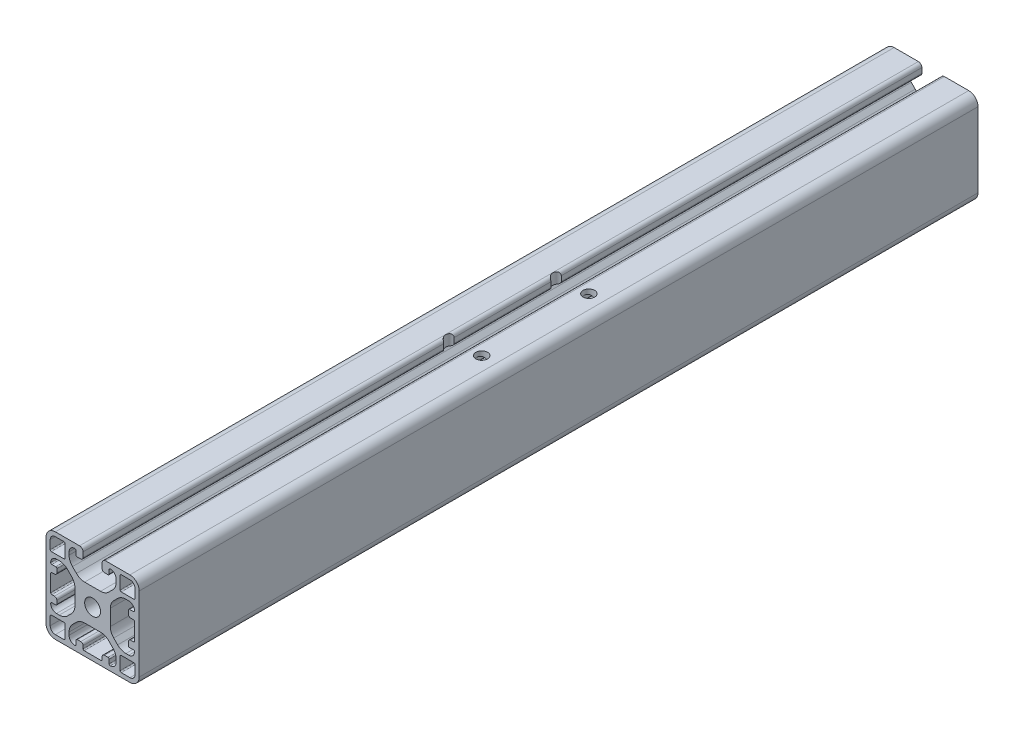
SolidWorks part; units mm, degrees
ref_plane "Ebene vorne" through (0, 0, 0) normal (0, 0, 1) x (1, 0, 0)
ref_plane "Ebene oben" through (0, 0, 0) normal (0, 1, 0) x (1, 0, 0)
ref_plane "Ebene rechts" through (0, 0, 0) normal (1, 0, 0) x (0, 0, -1)
ref_plane "Ebene1" through (0, 0, 1000) normal (0, 0, 1) x (1, 0, 0)
sketch "Skizze1" plane through (0, 0, 1000) normal (0, 0, 1) x (1, 0, 0)
  line L0 (0, 38.2) -> (3.7, 38.2)
  line L1 (4.2, 37.7) -> (4.2, 32.3)
  line L2 (3.7, 31.8) -> (-1.7, 31.8)
  line L3 (-2.2, 32.3) -> (-2.2, 36)
  line L4 (-2.2, 4) -> (-2.2, 7.7)
  line L5 (-1.7, 8.2) -> (3.7, 8.2)
  line L6 (4.2, 7.7) -> (4.2, 2.3)
  line L7 (3.7, 1.8) -> (0, 1.8)
  line L8 (32, 1.8) -> (28.3, 1.8)
  line L9 (27.8, 2.3) -> (27.8, 7.7)
  line L10 (28.3, 8.2) -> (33.7, 8.2)
  line L11 (34.2, 7.7) -> (34.2, 4)
  line L12 (34.2, 36) -> (34.2, 32.3)
  line L13 (33.7, 31.8) -> (28.3, 31.8)
  line L14 (27.8, 32.3) -> (27.8, 37.7)
  line L15 (28.3, 38.2) -> (32, 38.2)
  line L16 (12.5924, 12.4) -> (19.4076, 12.4)
  line L17 (22.9431, 10.9355) -> (24.6355, 9.2431)
  line L18 (26.1, 5.7076) -> (26.1, 4.5)
  line L19 (23.1, 2.5) -> (23.1, 4.15)
  line L20 (22.6, 4.65) -> (21.1, 4.65)
  line L21 (20.1, 3.65) -> (20.1, 2.5)
  line L22 (19.6, 2) -> (12.4, 2)
  line L23 (11.9, 2.5) -> (11.9, 3.65)
  line L24 (10.9, 4.65) -> (9.4, 4.65)
  line L25 (8.9, 4.15) -> (8.9, 2.5)
  line L26 (5.9, 4.5) -> (5.9, 5.7076)
  line L27 (7.3645, 9.2431) -> (9.0569, 10.9355)
  line L28 (-0.35, 15.9) -> (-1.5, 15.9)
  line L29 (-2, 16.4) -> (-2, 23.6)
  line L30 (-1.5, 24.1) -> (-0.35, 24.1)
  line L31 (0.65, 25.1) -> (0.65, 26.6)
  line L32 (0.15, 27.1) -> (-1.5, 27.1)
  line L33 (0.5, 30.1) -> (1.7076, 30.1)
  line L34 (5.2431, 28.6355) -> (6.9355, 26.9431)
  line L35 (8.4, 23.4076) -> (8.4, 16.5924)
  line L36 (6.9355, 13.0569) -> (5.2431, 11.3645)
  line L37 (1.7076, 9.9) -> (0.5, 9.9)
  line L38 (-1.5, 12.9) -> (0.15, 12.9)
  line L39 (0.65, 13.4) -> (0.65, 14.9)
  line L40 (23.6, 16.5924) -> (23.6, 23.4076)
  line L41 (25.0645, 26.9431) -> (26.7569, 28.6355)
  line L42 (30.2924, 30.1) -> (31.5, 30.1)
  line L43 (33.5, 27.1) -> (31.85, 27.1)
  line L44 (31.35, 26.6) -> (31.35, 25.1)
  line L45 (32.35, 24.1) -> (33.5, 24.1)
  line L46 (34, 23.6) -> (34, 16.4)
  line L47 (33.5, 15.9) -> (32.35, 15.9)
  line L48 (31.35, 14.9) -> (31.35, 13.4)
  line L49 (31.85, 12.9) -> (33.5, 12.9)
  line L50 (31.5, 9.9) -> (30.2924, 9.9)
  line L51 (26.7569, 11.3645) -> (25.0645, 13.0569)
  line L52 (23.1, 35.85) -> (23.1, 37.5)
  line L53 (26.1, 35.5) -> (26.1, 34.2924)
  line L54 (24.6355, 30.7569) -> (22.9431, 29.0645)
  line L55 (19.4076, 27.6) -> (12.5924, 27.6)
  line L56 (9.0569, 29.0645) -> (7.3645, 30.7569)
  line L57 (5.9, 34.2924) -> (5.9, 35.5)
  line L58 (8.9, 37.5) -> (8.9, 35.85)
  line L59 (9.4, 35.35) -> (10.9, 35.35)
  line L60 (11.9, 36.35) -> (11.9, 38.5)
  line L61 (10.4, 40) -> (0, 40)
  line L62 (-4, 36) -> (-4, 4)
  line L63 (0, 0) -> (32, 0)
  line L64 (36, 4) -> (36, 36)
  line L65 (32, 40) -> (21.6, 40)
  line L66 (20.1, 38.5) -> (20.1, 36.35)
  line L67 (21.1, 35.35) -> (22.6, 35.35)
  circle A0 centre (16, 20) radius 3.4
  arc A1 (3.7, 38.2) -> (4.2, 37.7) centre (3.7, 37.7) cw
  arc A2 (4.2, 32.3) -> (3.7, 31.8) centre (3.7, 32.3) cw
  arc A3 (-1.7, 31.8) -> (-2.2, 32.3) centre (-1.7, 32.3) cw
  arc A4 (-2.2, 36) -> (0, 38.2) centre (0, 36) cw
  arc A5 (-2.2, 7.7) -> (-1.7, 8.2) centre (-1.7, 7.7) cw
  arc A6 (3.7, 8.2) -> (4.2, 7.7) centre (3.7, 7.7) cw
  arc A7 (4.2, 2.3) -> (3.7, 1.8) centre (3.7, 2.3) cw
  arc A8 (0, 1.8) -> (-2.2, 4) centre (0, 4) cw
  arc A9 (28.3, 1.8) -> (27.8, 2.3) centre (28.3, 2.3) cw
  arc A10 (27.8, 7.7) -> (28.3, 8.2) centre (28.3, 7.7) cw
  arc A11 (33.7, 8.2) -> (34.2, 7.7) centre (33.7, 7.7) cw
  arc A12 (34.2, 4) -> (32, 1.8) centre (32, 4) cw
  arc A13 (34.2, 32.3) -> (33.7, 31.8) centre (33.7, 32.3) cw
  arc A14 (28.3, 31.8) -> (27.8, 32.3) centre (28.3, 32.3) cw
  arc A15 (27.8, 37.7) -> (28.3, 38.2) centre (28.3, 37.7) cw
  arc A16 (32, 38.2) -> (34.2, 36) centre (32, 36) cw
  arc A17 (19.4076, 12.4) -> (22.9431, 10.9355) centre (19.4076, 7.4) cw
  arc A18 (24.6355, 9.2431) -> (26.1, 5.7076) centre (21.1, 5.7076) cw
  arc A19 (26.1, 4.5) -> (23.6, 2) centre (23.6, 4.5) cw
  arc A20 (23.6, 2) -> (23.1, 2.5) centre (23.6, 2.5) cw
  arc A21 (23.1, 4.15) -> (22.6, 4.65) centre (22.6, 4.15) ccw
  arc A22 (21.1, 4.65) -> (20.1, 3.65) centre (21.1, 3.65) ccw
  arc A23 (20.1, 2.5) -> (19.6, 2) centre (19.6, 2.5) cw
  arc A24 (12.4, 2) -> (11.9, 2.5) centre (12.4, 2.5) cw
  arc A25 (11.9, 3.65) -> (10.9, 4.65) centre (10.9, 3.65) ccw
  arc A26 (9.4, 4.65) -> (8.9, 4.15) centre (9.4, 4.15) ccw
  arc A27 (8.9, 2.5) -> (8.4, 2) centre (8.4, 2.5) cw
  arc A28 (8.4, 2) -> (5.9, 4.5) centre (8.4, 4.5) cw
  arc A29 (5.9, 5.7076) -> (7.3645, 9.2431) centre (10.9, 5.7076) cw
  arc A30 (9.0569, 10.9355) -> (12.5924, 12.4) centre (12.5924, 7.4) cw
  arc A31 (-1.5, 15.9) -> (-2, 16.4) centre (-1.5, 16.4) cw
  arc A32 (-2, 23.6) -> (-1.5, 24.1) centre (-1.5, 23.6) cw
  arc A33 (-0.35, 24.1) -> (0.65, 25.1) centre (-0.35, 25.1) ccw
  arc A34 (0.65, 26.6) -> (0.15, 27.1) centre (0.15, 26.6) ccw
  arc A35 (-1.5, 27.1) -> (-2, 27.6) centre (-1.5, 27.6) cw
  arc A36 (-2, 27.6) -> (0.5, 30.1) centre (0.5, 27.6) cw
  arc A37 (1.7076, 30.1) -> (5.2431, 28.6355) centre (1.7076, 25.1) cw
  arc A38 (6.9355, 26.9431) -> (8.4, 23.4076) centre (3.4, 23.4076) cw
  arc A39 (8.4, 16.5924) -> (6.9355, 13.0569) centre (3.4, 16.5924) cw
  arc A40 (5.2431, 11.3645) -> (1.7076, 9.9) centre (1.7076, 14.9) cw
  arc A41 (0.5, 9.9) -> (-2, 12.4) centre (0.5, 12.4) cw
  arc A42 (-2, 12.4) -> (-1.5, 12.9) centre (-1.5, 12.4) cw
  arc A43 (0.15, 12.9) -> (0.65, 13.4) centre (0.15, 13.4) ccw
  arc A44 (0.65, 14.9) -> (-0.35, 15.9) centre (-0.35, 14.9) ccw
  arc A45 (23.6, 23.4076) -> (25.0645, 26.9431) centre (28.6, 23.4076) cw
  arc A46 (26.7569, 28.6355) -> (30.2924, 30.1) centre (30.2924, 25.1) cw
  arc A47 (31.5, 30.1) -> (34, 27.6) centre (31.5, 27.6) cw
  arc A48 (34, 27.6) -> (33.5, 27.1) centre (33.5, 27.6) cw
  arc A49 (31.85, 27.1) -> (31.35, 26.6) centre (31.85, 26.6) ccw
  arc A50 (31.35, 25.1) -> (32.35, 24.1) centre (32.35, 25.1) ccw
  arc A51 (33.5, 24.1) -> (34, 23.6) centre (33.5, 23.6) cw
  arc A52 (34, 16.4) -> (33.5, 15.9) centre (33.5, 16.4) cw
  arc A53 (32.35, 15.9) -> (31.35, 14.9) centre (32.35, 14.9) ccw
  arc A54 (31.35, 13.4) -> (31.85, 12.9) centre (31.85, 13.4) ccw
  arc A55 (33.5, 12.9) -> (34, 12.4) centre (33.5, 12.4) cw
  arc A56 (34, 12.4) -> (31.5, 9.9) centre (31.5, 12.4) cw
  arc A57 (30.2924, 9.9) -> (26.7569, 11.3645) centre (30.2924, 14.9) cw
  arc A58 (25.0645, 13.0569) -> (23.6, 16.5924) centre (28.6, 16.5924) cw
  arc A59 (22.6, 35.35) -> (23.1, 35.85) centre (22.6, 35.85) ccw
  arc A60 (23.1, 37.5) -> (23.6, 38) centre (23.6, 37.5) cw
  arc A61 (23.6, 38) -> (26.1, 35.5) centre (23.6, 35.5) cw
  arc A62 (26.1, 34.2924) -> (24.6355, 30.7569) centre (21.1, 34.2924) cw
  arc A63 (22.9431, 29.0645) -> (19.4076, 27.6) centre (19.4076, 32.6) cw
  arc A64 (12.5924, 27.6) -> (9.0569, 29.0645) centre (12.5924, 32.6) cw
  arc A65 (7.3645, 30.7569) -> (5.9, 34.2924) centre (10.9, 34.2924) cw
  arc A66 (5.9, 35.5) -> (8.4, 38) centre (8.4, 35.5) cw
  arc A67 (8.4, 38) -> (8.9, 37.5) centre (8.4, 37.5) cw
  arc A68 (8.9, 35.85) -> (9.4, 35.35) centre (9.4, 35.85) ccw
  arc A69 (10.9, 35.35) -> (11.9, 36.35) centre (10.9, 36.35) ccw
  arc A70 (11.9, 38.5) -> (10.4, 40) centre (10.4, 38.5) ccw
  arc A71 (0, 40) -> (-4, 36) centre (0, 36) ccw
  arc A72 (-4, 4) -> (0, 0) centre (0, 4) ccw
  arc A73 (32, 0) -> (36, 4) centre (32, 4) ccw
  arc A74 (36, 36) -> (32, 40) centre (32, 36) ccw
  arc A75 (21.6, 40) -> (20.1, 38.5) centre (21.6, 38.5) ccw
  arc A76 (20.1, 36.35) -> (21.1, 35.35) centre (21.1, 36.35) ccw
extrude "Aufsatz-Linear austragen1" add sketch "Skizze1" against normal blind 360
hole_wizard "M6 Gewindebohrung1" positions "Skizze2" profile "Skizze3" tap size "M6" standard "DIN" end condition through all
sketch "Skizze2" plane through (0, 0, 0) normal (0, -1, 0) x (-1, 0, 0)
  point P0 (-26, -797)
  point P3 (-13, -797)
  point P6 (-26, -843)
  point P9 (-13, -843)
sketch "Skizze3" plane through (26, 0, 797) normal (1, 0, 0) x (0, 0, -1)
  line L0 (0, 0) -> (0, 40)
  line L1 (0, 40) -> (2.5, 40)
  line L2 (2.5, 40) -> (2.5, 0)
  line L5 (2.5, 0) -> (0, 0)
  line L11 (0, -6.35) -> (0, 107.95) construction
  dimension "Bohrerdurchmesser" = 5
  dimension "Bohrungstiefe" = 40
cosmetic thread "Bohrungsgewinde1" parameters "D2"=6
cosmetic thread "Bohrungsgewinde2" parameters "D2"=6
cosmetic thread "Bohrungsgewinde3" parameters "D2"=6
cosmetic thread "Bohrungsgewinde4" parameters "D2"=6
